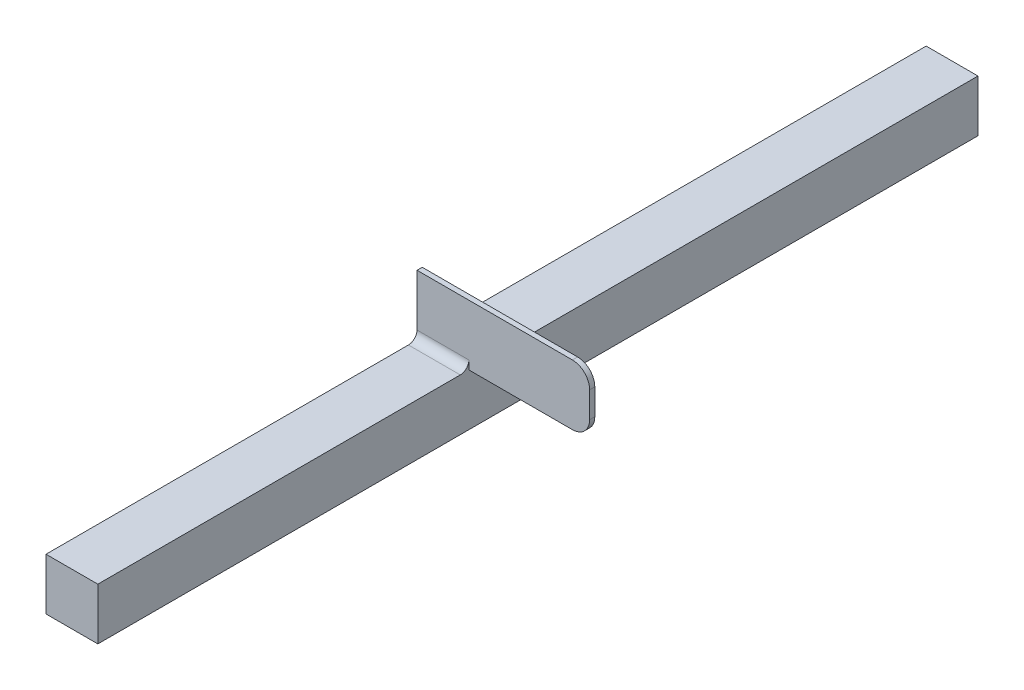
SolidWorks part; units mm, degrees
ref_plane "Plano frontal" through (0, 0, 0) normal (0, 0, 1) x (1, 0, 0)
ref_plane "Plano superior" through (0, 0, 0) normal (0, 1, 0) x (1, 0, 0)
ref_plane "Plano direito" through (0, 0, 0) normal (1, 0, 0) x (0, 0, -1)
sketch "Esboço2" plane through (0, 0, 0) normal (0, 0, 1) x (1, 0, 0)
  line L1 (-110.6583, 30) -> (-80.6129, 30)
  line L2 (-110.6583, 30) -> (-110.6583, 0)
  line L3 (-110.6583, 0) -> (-80.6129, 0)
  line L4 (-80.6129, 30) -> (-80.6129, 0)
  dimension "D1" = 30
  dimension "D2" = 30.0454
extrude "Ressalto-extrusão1" add sketch "Esboço2" along normal mid plane 510
ref_plane "Plano1" through (0, 0, 40) normal (0, 0, 1) x (1, 0, 0)
sketch "Esboço4" plane through (0, 0, 40) normal (0, 0, 1) x (1, 0, 0)
  line L1 (-10.6583, 30) -> (-110.6583, 30)
  line L2 (-10.6583, 30) -> (-10.6583, 65)
  line L3 (-10.6583, 65) -> (-110.6583, 65)
  line L4 (-110.6583, 30) -> (-110.6583, 65)
  point P5 (0, 0)
  point P6 (0, 0)
  point P7 (0, 0)
  dimension "D1" = 35
  dimension "D2" = 100
extrude "Ressalto-extrusão2" add sketch "Esboço4" along normal blind 0.001 and the other way blind 3
fillet "Filete1" radius 5 2 edges at (-95.6356, 30, 37) (-95.6356, 30, 40.001)
fillet "Filete2" radius 10 2 edges at (-10.6583, 65, 38.5005) (-10.6583, 30, 38.5005)
